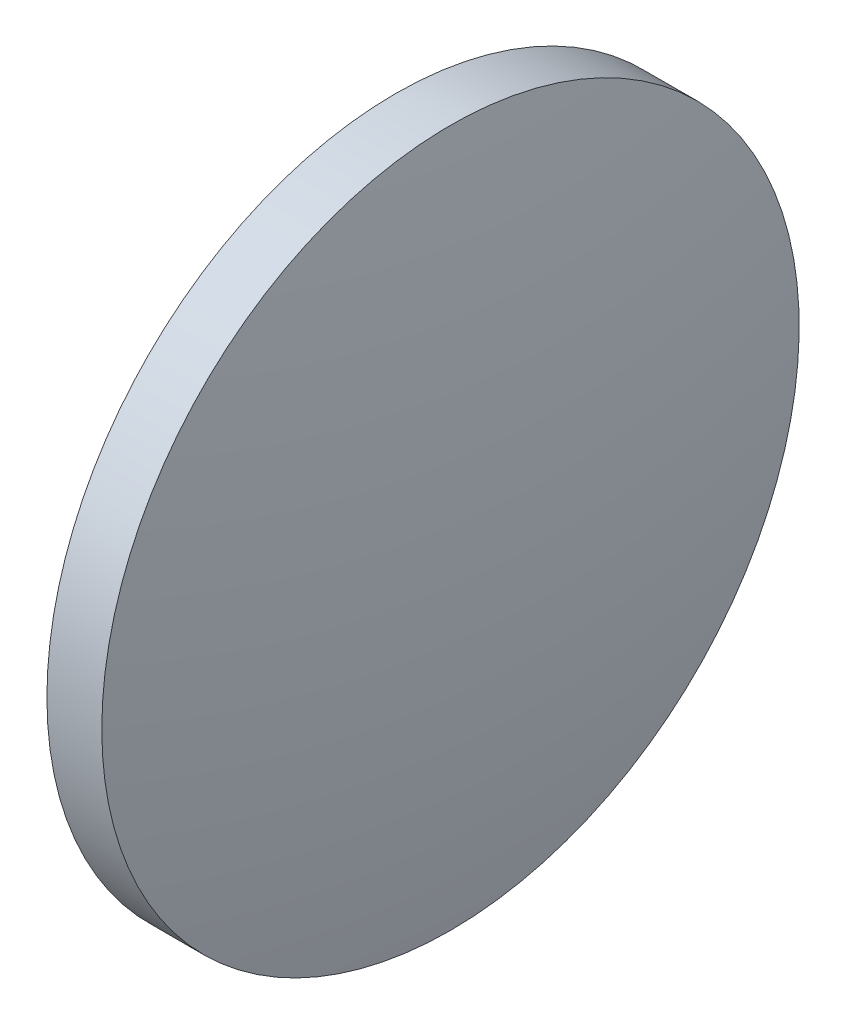
SolidWorks part; units mm, degrees
ref_plane "前视基准面" through (0, 0, 0) normal (0, 0, 1) x (1, 0, 0)
ref_plane "上视基准面" through (0, 0, 0) normal (0, 1, 0) x (1, 0, 0)
ref_plane "右视基准面" through (0, 0, 0) normal (1, 0, 0) x (0, 0, -1)
sketch "草图1" plane through (0, 0, 0) normal (0, 0, 1) x (1, 0, 0)
  line L0 (79.3054, 48.6161) -> (93.4772, 48.6161) construction
  line L1 (85.4585, 61.3161) -> (87.4579, 61.3161)
  line L2 (87.4579, 61.3161) -> (87.4579, 35.9161)
  line L3 (87.4579, 35.9161) -> (85.4585, 35.9161)
  line L4 (85.4585, 35.9161) -> (85.4585, 61.3161)
  arc A0 (85.4585, 61.3161) -> (85.4585, 35.9161) centre (154.9916, 48.6161) ccw
  arc A1 (87.4579, 35.9161) -> (87.4579, 61.3161) centre (17.9248, 48.6161) ccw
  dimension "D1" = 25.4
  dimension "D2" = 1.9993
revolve "旋转1" add sketch "草图1" angle 360 about L0
